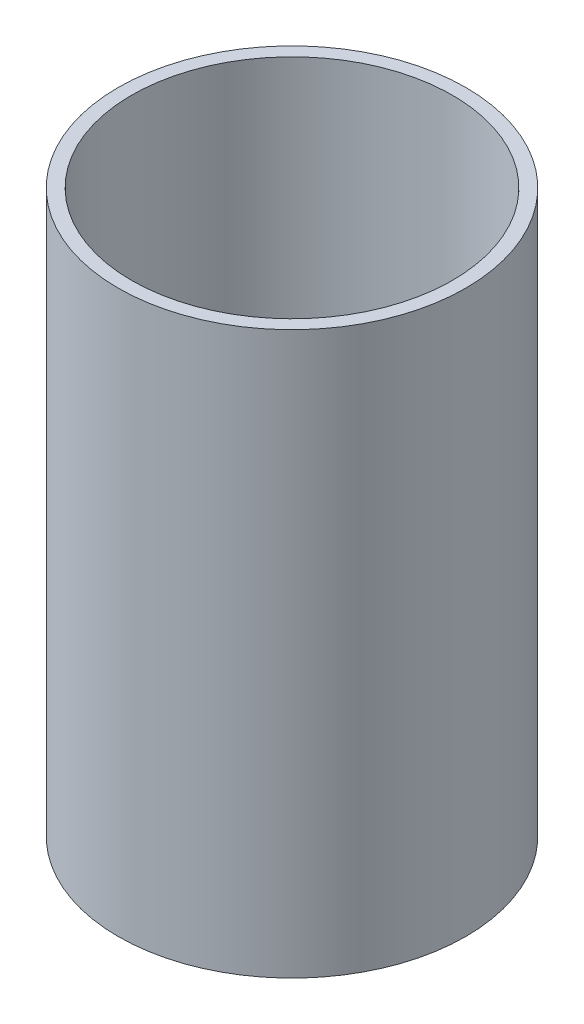
SolidWorks part; units mm, degrees
material "PTFE (general)"
ref_plane "Front Plane" through (0, 0, 0) normal (0, 0, 1) x (1, 0, 0)
ref_plane "Top Plane" through (0, 0, 0) normal (0, 1, 0) x (1, 0, 0)
ref_plane "Right Plane" through (0, 0, 0) normal (1, 0, 0) x (0, 0, -1)
ref_axis "Axis1" through (0, 55, 0) along (0, -1, 0)
sketch "Sketch2" plane through (0, 0, 0) normal (0, 0, 1) x (1, 0, 0)
  line L1 (-41.275, 0) -> (-38.1, 0)
  line L2 (-41.275, 0) -> (-41.275, -133.35)
  line L3 (-41.275, -133.35) -> (-38.1, -133.35)
  line L4 (-38.1, 0) -> (-38.1, -133.35)
  dimension "D2" = 3.175
revolve "Revolve1" add sketch "Sketch2" angle 360 about axis through (0, 55, 0) along (0, -1, 0)
equation "\"D2@Sketch2\"=\"LINER THICKNESS@Cryo Tank.Assembly\""
